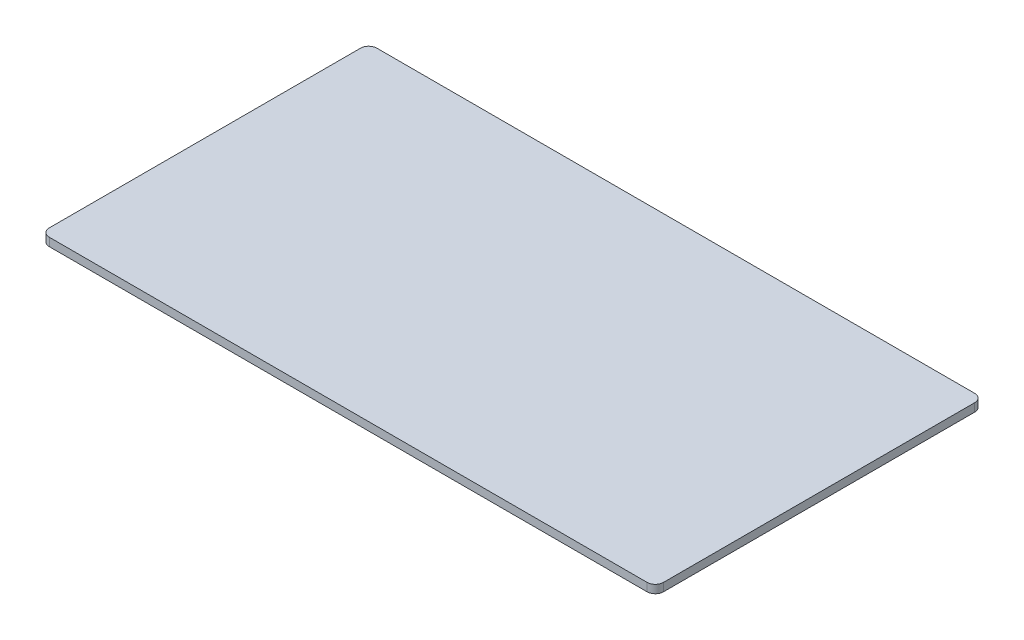
SolidWorks part; units mm, degrees
material "Plain Carbon Steel"
ref_plane "Front Plane" through (0, 0, 0) normal (0, 0, 1) x (1, 0, 0)
ref_plane "Top Plane" through (0, 0, 0) normal (0, 1, 0) x (1, 0, 0)
ref_plane "Right Plane" through (0, 0, 0) normal (1, 0, 0) x (0, 0, -1)
sketch "Sketch2" plane through (0, 0, 0) normal (0, 1, 0) x (1, 0, 0)
  line L1 (-750, 400) -> (750, 400)
  line L2 (-750, 400) -> (-750, -400)
  line L3 (-750, -400) -> (750, -400)
  line L4 (750, 400) -> (750, -400)
  line L5 (-750, 400) -> (750, -400) construction
  line L6 (-750, -400) -> (750, 400) construction
  point P0 (0, 0)
  dimension "D1" = 1500
  dimension "D2" = 800
extrude "Boss-Extrude1" add sketch "Sketch2" along normal mid plane 20
fillet "Fillet1" radius 20 4 edges at (-750, 0, 400) (750, 0, 400) (750, 0, -400) (-750, 0, -400)
